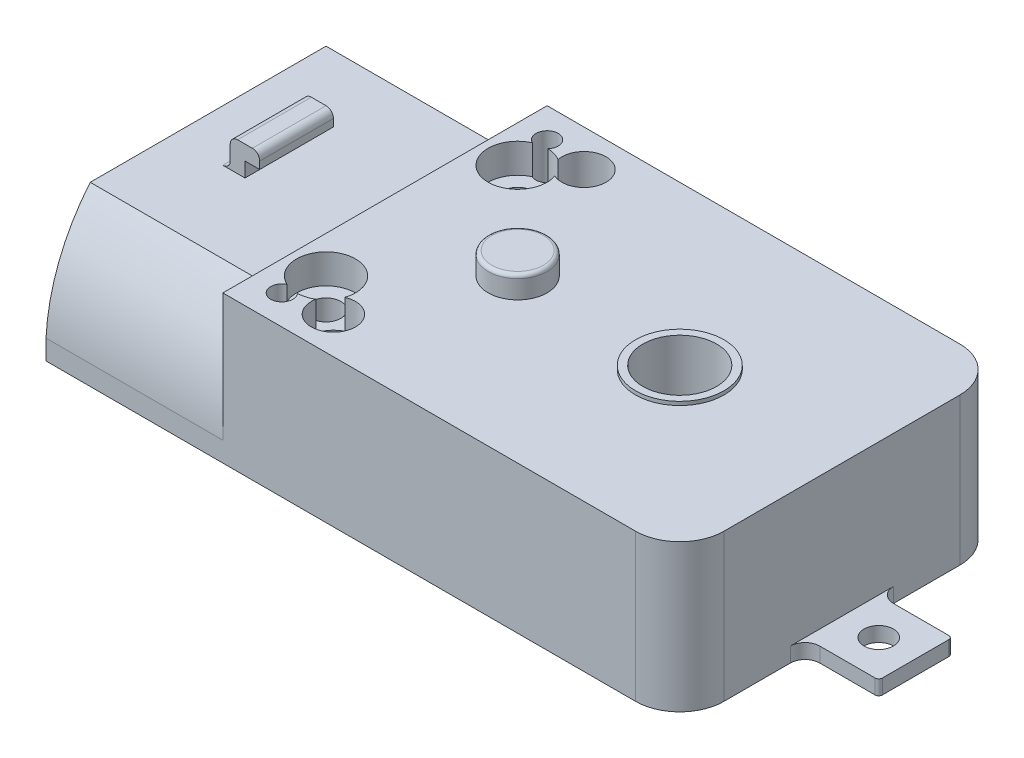
SolidWorks part; units mm, degrees
ref_plane "Front Plane" through (0, 0, 0) normal (0, 0, 1) x (1, 0, 0)
ref_plane "Top Plane" through (0, 0, 0) normal (0, 1, 0) x (1, 0, 0)
ref_plane "Right Plane" through (0, 0, 0) normal (1, 0, 0) x (0, 0, -1)
sketch "Sketch2" plane through (0, 0, 0) normal (0, 1, 0) x (1, 0, 0)
  line L0 (31, 11) -> (0, 11) construction
  line L1 (0, 0) -> (31, 0)
  line L2 (0, 0) -> (0, 22)
  line L3 (0, 22) -> (31, 22)
  line L4 (31, 0) -> (31, 22)
  line L7 (31, 8.5) -> (31, 13.5)
  dimension "48" = 31
  dimension "22" = 22
extrude "Boss-Extrude2" add sketch "Sketch2" along normal blind 9 contours L0 L7 L4 L3 L2 | L4 L0 L2 L1
sketch "Sketch4" plane through (31, 0, 0) normal (1, 0, 0) x (0, 0, -1)
  line L0 (0, 0) -> (22, 0) construction
  line L1 (8.5, 0) -> (13.5, 0)
  line L2 (8.5, 0) -> (8.5, 1)
  line L3 (8.5, 1) -> (13.5, 1)
  line L4 (13.5, 0) -> (13.5, 1)
  point P6 (11, 1)
  dimension "D1" = 1
  dimension "D2" = 5
  dimension "D3" = 11
extrude "Boss-Extrude3" add sketch "Sketch4" along normal blind 5
sketch "Sketch5" plane through (0, 1, 0) normal (0, 1, 0) x (1, 0, 0)
  circle A0 centre (33.5, 11) radius 1
  dimension "D1" = 2
  dimension "D2" = 2.5
  dimension "D3" = 2.5
extrude "Cut-Extrude1" cut sketch "Sketch5" against normal blind 5
fillet "Fillet1" radius 1 1 edges
fillet "Fillet2" radius 1 1 edges
fillet "Fillet3" radius 3 1 edges at (31, 4.5, 0)
fillet "Fillet4" radius 3 1 edges at (31, 4.5, -22)
sketch "Sketch6" plane through (0, 0, 0) normal (-1, 0, 0) x (0, 0, 1)
  line L0 (-11, 0) -> (-11, 9) construction
  line L1 (0, 0) -> (-22, 0) construction
  line L2 (0, 9) -> (-22, 9) construction
  line L3 (-22, 0) -> (0, 0)
  line L5 (-22, 0) -> (-22.0206, -0.0102)
  line L6 (0, 1.3449) -> (0, 0)
  line L7 (-19, 9) -> (-3, 9)
  line L8 (0, 0) -> (-22, 0)
  arc A0 (0, 0) -> (-3, 9) centre (-12.9826, 0.6725) ccw
  arc A1 (-22, 0) -> (-19, 9) centre (-9.0174, 0.6725) cw
  point P9 (0, 0)
  line M1 (-22, 0) -> (0, 0)
  line M2 (0, 0) -> (0, 9)
  line M3 (0, 9) -> (-22, 9)
  line M4 (-22, 9) -> (-22, 0)
  dimension "D1" = 13
  dimension "D2" = 3
sketch "Sketch7" plane through (0, 0, 0) normal (-1, 0, 0) x (0, 0, 1)
extrude "Boss-Extrude4" add sketch "Sketch6" along normal blind 12 contours L0 L7 A1 M1 M4 | L0 L8 A0 M2 M3
fillet "Fillet6" radius 0.25 2 edges at (36, 0.5, -13.5) (36, 0.5, -8.5)
sketch "Sketch10" plane through (0, 9, 0) normal (0, 1, 0) x (1, 0, 0)
  line L3 (0, 3) -> (0, 0) construction
  line L5 (0, 0) -> (28, 0) construction
  circle A0 centre (5, 19.5) radius 1.5
  circle A1 centre (5, 2.5) radius 1.5
  dimension "D3" = 2.5
  dimension "D1" = 3
  dimension "D2" = 5
extrude "Cut-Extrude7" cut sketch "Sketch10" against normal through all both and the other way through all
sketch "Sketch12" plane through (0, 9, 0) normal (0, 1, 0) x (1, 0, 0)
  line L1 (0, 22) -> (0, 19) construction
  line L2 (0, 3) -> (0, 0) construction
  line L3 (0, 0) -> (28, 0) construction
  circle A0 centre (2, 2) radius 0.75
  circle A1 centre (2, 20) radius 0.75
  dimension "D1" = 1.5
  dimension "D2" = 1.5
  dimension "D3" = 2
  dimension "D4" = 2
  dimension "D5" = 2
  dimension "D6" = 2
extrude "Cut-Extrude8" cut sketch "Sketch12" against normal blind 3
sketch "Sketch13" plane through (0, 9, 0) normal (0, 1, 0) x (1, 0, 0)
  line L0 (-12, 11) -> (36, 11) construction
  line L1 (-8, 13.5) -> (-7, 13.5)
  line L2 (-8, 13.5) -> (-8, 8.5)
  line L3 (-8, 8.5) -> (-7, 8.5)
  line L4 (-7, 13.5) -> (-7, 8.5)
  line L5 (-12, 3) -> (-12, 19) construction
  line L6 (36, 13.25) -> (36, 8.75) construction
  dimension "D1" = 4
  dimension "D2" = 1
  dimension "D3" = 5
  dimension "D4" = 2.5
extrude "Boss-Extrude5" add sketch "Sketch13" along normal blind 2
sketch "Sketch14" plane through (-7, 0, 0) normal (1, 0, 0) x (0, 0, -1)
  line L0 (13.5, 11) -> (13.5, 9) construction
  line L1 (8.5, 11) -> (13.5, 11)
  line L2 (8.5, 11) -> (8.5, 10)
  line L3 (8.5, 10) -> (13.5, 10)
  line L4 (13.5, 11) -> (13.5, 10)
extrude "Boss-Extrude6" add sketch "Sketch14" along normal blind 1
fillet "Fillet7" radius 0.5 1 edges at (-8, 11, -11)
fillet "Fillet8" radius 0.5 1 edges at (-8, 9, -11)
fillet "Fillet9" radius 0.5 1 edges at (-6, 11, -11)
sketch "Sketch16" plane through (-12, 0, 0) normal (-1, 0, 0) x (0, 0, 1)
  line L0 (-18.2321, 8.3594) -> (-3.7679, 8.3594)
  line L1 (-21.0013, 1.2932) -> (-21, 0)
  line L2 (-0.9987, 1.2932) -> (-0.9987, 0)
  line L3 (-21, 0) -> (-0.9987, 0)
  arc A2 (-18.2321, 8.3594) -> (-21.0013, 1.2932) centre (-9.0174, 0.6725) ccw
  arc A3 (-18.2321, 8.3594) -> (-21.0013, 1.2932) centre (-9.0174, 0.6725) ccw
  arc A5 (-0.9987, 1.2932) -> (-3.7679, 8.3594) centre (-12.9826, 0.6725) ccw
  arc A6 (-0.9987, 1.2932) -> (-3.7679, 8.3594) centre (-12.9826, 0.6725) ccw
  dimension "D1" = 1
  dimension "D2" = 1
extrude "Cut-Extrude9" cut sketch "Sketch16" against normal blind 10
sketch "Sketch17" plane through (0, 9, 0) normal (0, 1, 0) x (1, 0, 0)
  line L0 (0, 3) -> (0, 19)
  line L8 (31, 3) -> (31, 19)
  line L9 (28, 22) -> (0, 22)
  line L10 (0, 22) -> (0, 19)
  line L11 (0, 19) -> (-12, 19)
  line L12 (-12, 19) -> (-12, 3)
  line L13 (-12, 3) -> (0, 3)
  line L14 (0, 3) -> (0, 0)
  line L15 (0, 0) -> (28, 0)
  line L16 (31, 3) -> (31, 19)
  line L17 (28, 22) -> (0, 22)
  line L18 (0, 22) -> (0, 19)
  line L22 (0, 3) -> (0, 0)
  line L23 (0, 0) -> (28, 0)
  arc A2 (31, 19) -> (28, 22) centre (28, 19) ccw
  arc A3 (28, 0) -> (31, 3) centre (28, 3) ccw
  arc A4 (31, 19) -> (28, 22) centre (28, 19) ccw
  arc A5 (28, 0) -> (31, 3) centre (28, 3) ccw
  dimension "D1" = 0
extrude "Boss-Extrude7" add sketch "Sketch17" along normal blind 1
sketch "Sketch18" plane through (0, 10, 0) normal (0, 1, 0) x (1, 0, 0)
  line L0 (0, 11) -> (31, 11) construction
  line L1 (0, 19) -> (0, 3) construction
  line L2 (31, 3) -> (31, 19) construction
  circle A1 centre (5, 19.5) radius 1.5
  circle A3 centre (5, 2.5) radius 1.5
  dimension "D3" = 2.5
  dimension "D8" = 5
  dimension "3" = 3
  dimension "D10" = 3
  dimension "D2" = 2.5
  dimension "D9" = 5
extrude "Cut-Extrude12" cut sketch "Sketch18" against normal through all
sketch "Sketch19" plane through (0, 10, 0) normal (0, 1, 0) x (1, 0, 0)
  line L0 (0, 11) -> (31, 11) construction
  line L1 (0, 22) -> (0, 0) construction
  line L2 (31, 3) -> (31, 19) construction
  circle A0 centre (2, 20) radius 0.75
  circle A1 centre (2, 2) radius 0.75
  dimension "D1" = 1.5
  dimension "D2" = 1.5
  dimension "D3" = 2
  dimension "2" = 2
  dimension "D4" = 2
  dimension "D5" = 2
extrude "Cut-Extrude14" cut sketch "Sketch19" against normal through all
sketch "Sketch20" plane through (0, 10, 0) normal (0, 1, 0) x (1, 0, 0)
  line L0 (0, 11) -> (31, 11) construction
  line L1 (0, 22) -> (0, 0) construction
  line L2 (31, 3) -> (31, 19) construction
  circle A0 centre (9, 11) radius 2
  dimension "D2" = 4
  dimension "D1" = 22
extrude "Boss-Extrude8" add sketch "Sketch20" along normal blind 1.5
fillet "Fillet10" radius 0.25 1 edges at (9, 11.5, -9)
sketch "Sketch21" plane through (0, 10, 0) normal (0, 1, 0) x (1, 0, 0)
  line L0 (0, 11) -> (31, 11) construction
  line L1 (0, 19) -> (0, 3) construction
  line L2 (31, 3) -> (31, 19) construction
  circle A0 centre (20, 11) radius 2.5
  dimension "D1" = 11
  dimension "6" = 5
extrude "Cut-Extrude15" cut sketch "Sketch21" against normal blind 5
sketch "Sketch22" plane through (0, 10, 0) normal (0, 1, 0) x (1, 0, 0)
  circle A0 centre (20, 11) radius 3
  circle A1 centre (20, 11) radius 2.5
  dimension "D1" = 6
  dimension "D2" = 5
extrude "Boss-Extrude9" add sketch "Sketch22" along normal blind 0.25
sketch "Sketch24" plane through (0, 10, 0) normal (0, 1, 0) x (1, 0, 0)
  line L0 (0, 11) -> (36, 11) construction
  line L1 (0, 19) -> (0, 3) construction
  line L2 (36, 13.25) -> (36, 8.75) construction
  circle A0 centre (2.5, 17.5) radius 2
  circle A1 centre (2.5, 4.5) radius 2
  dimension "D1" = 4
  dimension "D2" = 2.5
  dimension "D3" = 4.5
extrude "Cut-Extrude16" cut sketch "Sketch24" against normal blind 2
sketch "Sketch25" plane through (0, 10, 0) normal (0, 1, 0) x (1, 0, 0)
  circle A0 centre (2.5, 17.5) radius 1
  circle A1 centre (2.5, 4.5) radius 1
  dimension "D1" = 2
  dimension "D2" = 2
extrude "Cut-Extrude17" cut sketch "Sketch25" against normal blind 5
